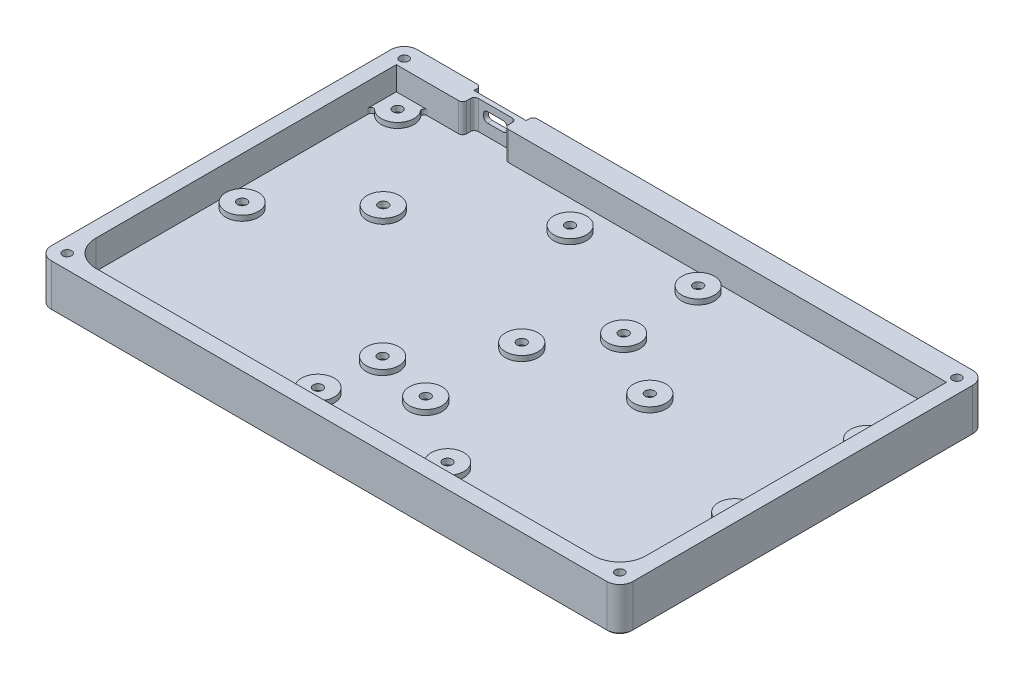
SolidWorks part; units mm, degrees
ref_plane "Front Plane" through (0, 0, 0) normal (0, 0, 1) x (1, 0, 0)
ref_plane "Top Plane" through (0, 0, 0) normal (0, 1, 0) x (1, 0, 0)
ref_plane "Right Plane" through (0, 0, 0) normal (1, 0, 0) x (0, 0, -1)
sketch "Sketch1" plane through (0, 0, 0) normal (0, 1, 0) x (1, 0, 0)
  line L1 (0, 0) -> (222.53, 0)
  line L2 (0, 0) -> (0, 140)
  line L3 (0, 140) -> (222.53, 140)
  line L4 (222.53, 0) -> (222.53, 140)
  dimension "D1" = 140
  dimension "D2" = 222.53
extrude "Baseplate" add sketch "Sketch1" along normal blind 5.6
sketch "Sketch2" plane through (0, 5.6, 0) normal (0, 1, 0) x (1, 0, 0)
  line L1 (0, 140) -> (222.53, 140)
  line L2 (0, 140) -> (0, 0)
  line L3 (0, 0) -> (222.53, 0)
  line L4 (222.53, 140) -> (222.53, 0)
  line L5 (206.53, 6) -> (16, 6)
  line L6 (216.53, 16) -> (216.53, 131)
  line L7 (216.53, 131) -> (6, 131)
  line L8 (6, 16) -> (6, 131)
  arc A0 (206.53, 6) -> (216.53, 16) centre (206.53, 16) ccw
  arc A1 (16, 6) -> (6, 16) centre (16, 16) cw
  dimension "D5" = 10
  dimension "D1" = 6
  dimension "D2" = 6
  dimension "D3" = 6
  dimension "D4" = 9
extrude "Sidewalls" add sketch "Sketch2" along normal blind 11
sketch "Sketch3" plane through (0, 16.6, 0) normal (0, 1, 0) x (1, 0, 0)
  line L0 (216.53, 131) -> (6, 131) construction
  line L1 (31.38, 131) -> (47.38, 131)
  line L2 (31.38, 131) -> (31.38, 135.5)
  line L3 (31.38, 135.5) -> (47.38, 135.5)
  line L4 (47.38, 131) -> (47.38, 135.5)
  line L5 (0, 140) -> (0, 0) construction
  line L7 (39.38, 135.5) -> (39.38, 131) construction
  dimension "D1" = 16
  dimension "D2" = 4.5
  dimension "D3" = 39.38
extrude "USB Relief" cut sketch "Sketch3" against normal up to surface (11 mm away) up to face at (111.265, 5.6, -50.3096)
sketch "Sketch6" plane through (0, 5.6, 0) normal (0, 1, 0) x (1, 0, 0)
  circle A0 centre (12, 125.5) radius 6.25
  circle A1 centre (83.5, 120) radius 6.25
  circle A2 centre (41, 91) radius 6.25
  circle A3 centre (13, 65) radius 6.25
  circle A4 centre (91, 40.75) radius 6.25
  circle A5 centre (138.5, 18.125) radius 6.25
  circle A6 centre (89, 18) radius 6.25
  circle A7 centre (112.5, 35.75) radius 6.25
  circle A8 centre (113, 72) radius 6.25
  circle A9 centre (210, 56.5) radius 6.25
  circle A10 centre (154.5, 79.5) radius 6.25
  circle A11 centre (211, 106) radius 6.25
  circle A12 centre (128, 124.5) radius 6.25
  circle A13 centre (129.5, 94.5) radius 6.25
  dimension "D1" = 12.5
extrude "PCB Support" add sketch "Sketch6" along normal blind 2
sketch "Sketch15" plane through (0, 5.6, 0) normal (0, 1, 0) x (1, 0, 0)
  line L1 (6, 131) -> (12, 131)
  line L2 (6, 131) -> (6, 125.5)
  line L3 (6, 125.5) -> (12, 125.5)
  line L4 (12, 131) -> (12, 125.5)
  arc A0 (6, 123.75) -> (14.9686, 131) centre (12, 125.5) ccw construction
extrude "Corner Fill" add sketch "Sketch15" along normal up to vertex
fillet "Fillet3" radius 1 2 edges at (6, 6.6, -123.75) (14.9686, 6.6, -131)
sketch "Sketch4" plane through (0, 5.6, 0) normal (0, 1, 0) x (1, 0, 0)
  line L1 (9.1, 128.4) -> (14.9, 128.4)
  line L2 (9.1, 128.4) -> (9.1, 122.6)
  line L3 (9.1, 122.6) -> (14.9, 122.6)
  line L4 (14.9, 128.4) -> (14.9, 122.6)
  line L5 (9.1, 128.4) -> (14.9, 122.6) construction
  line L6 (9.1, 122.6) -> (14.9, 128.4) construction
  line L7 (80.6, 122.9) -> (86.4, 122.9)
  line L8 (80.6, 122.9) -> (80.6, 117.1)
  line L9 (80.6, 117.1) -> (86.4, 117.1)
  line L10 (86.4, 122.9) -> (86.4, 117.1)
  line L11 (80.6, 122.9) -> (86.4, 117.1) construction
  line L12 (80.6, 117.1) -> (86.4, 122.9) construction
  line L13 (10.1, 62.1) -> (15.9, 62.1)
  line L14 (10.1, 62.1) -> (10.1, 67.9)
  line L15 (10.1, 67.9) -> (15.9, 67.9)
  line L16 (15.9, 62.1) -> (15.9, 67.9)
  line L17 (10.1, 62.1) -> (15.9, 67.9) construction
  line L18 (10.1, 67.9) -> (15.9, 62.1) construction
  line L19 (88.1, 37.85) -> (93.9, 37.85)
  line L20 (88.1, 37.85) -> (88.1, 43.65)
  line L21 (88.1, 43.65) -> (93.9, 43.65)
  line L22 (93.9, 37.85) -> (93.9, 43.65)
  line L23 (88.1, 37.85) -> (93.9, 43.65) construction
  line L24 (88.1, 43.65) -> (93.9, 37.85) construction
  line L25 (110.1, 69.1) -> (115.9, 69.1)
  line L26 (110.1, 69.1) -> (110.1, 74.9)
  line L27 (110.1, 74.9) -> (115.9, 74.9)
  line L28 (115.9, 69.1) -> (115.9, 74.9)
  line L29 (110.1, 69.1) -> (115.9, 74.9) construction
  line L30 (110.1, 74.9) -> (115.9, 69.1) construction
  line L31 (135.6, 15.225) -> (141.4, 15.225)
  line L32 (135.6, 15.225) -> (135.6, 21.025)
  line L33 (135.6, 21.025) -> (141.4, 21.025)
  line L34 (141.4, 15.225) -> (141.4, 21.025)
  line L35 (135.6, 15.225) -> (141.4, 21.025) construction
  line L36 (135.6, 21.025) -> (141.4, 15.225) construction
  line L37 (91.9, 15.1) -> (86.1, 15.1)
  line L38 (91.9, 15.1) -> (91.9, 20.9)
  line L39 (91.9, 20.9) -> (86.1, 20.9)
  line L40 (86.1, 15.1) -> (86.1, 20.9)
  line L41 (91.9, 15.1) -> (86.1, 20.9) construction
  line L42 (91.9, 20.9) -> (86.1, 15.1) construction
  line L43 (212.9, 59.4) -> (207.1, 59.4)
  line L44 (212.9, 59.4) -> (212.9, 53.6)
  line L45 (212.9, 53.6) -> (207.1, 53.6)
  line L46 (207.1, 59.4) -> (207.1, 53.6)
  line L47 (212.9, 59.4) -> (207.1, 53.6) construction
  line L48 (212.9, 53.6) -> (207.1, 59.4) construction
  line L49 (126.6, 91.6) -> (132.4, 91.6)
  line L50 (126.6, 91.6) -> (126.6, 97.4)
  line L51 (126.6, 97.4) -> (132.4, 97.4)
  line L52 (132.4, 91.6) -> (132.4, 97.4)
  line L53 (126.6, 91.6) -> (132.4, 97.4) construction
  line L54 (126.6, 97.4) -> (132.4, 91.6) construction
  line L55 (125.1, 127.4) -> (130.9, 127.4)
  line L56 (125.1, 127.4) -> (125.1, 121.6)
  line L57 (125.1, 121.6) -> (130.9, 121.6)
  line L58 (130.9, 127.4) -> (130.9, 121.6)
  line L59 (125.1, 127.4) -> (130.9, 121.6) construction
  line L60 (125.1, 121.6) -> (130.9, 127.4) construction
  line L61 (213.9, 103.1) -> (208.1, 103.1)
  line L62 (213.9, 103.1) -> (213.9, 108.9)
  line L63 (213.9, 108.9) -> (208.1, 108.9)
  line L64 (208.1, 103.1) -> (208.1, 108.9)
  line L65 (213.9, 103.1) -> (208.1, 108.9) construction
  line L66 (213.9, 108.9) -> (208.1, 103.1) construction
  line L67 (38.1, 88.1) -> (43.9, 88.1)
  line L68 (38.1, 88.1) -> (38.1, 93.9)
  line L69 (38.1, 93.9) -> (43.9, 93.9)
  line L70 (43.9, 88.1) -> (43.9, 93.9)
  line L71 (38.1, 88.1) -> (43.9, 93.9) construction
  line L72 (38.1, 93.9) -> (43.9, 88.1) construction
  line L73 (109.6, 32.85) -> (115.4, 32.85)
  line L74 (109.6, 32.85) -> (109.6, 38.65)
  line L75 (109.6, 38.65) -> (115.4, 38.65)
  line L76 (115.4, 32.85) -> (115.4, 38.65)
  line L77 (109.6, 32.85) -> (115.4, 38.65) construction
  line L78 (109.6, 38.65) -> (115.4, 32.85) construction
  line L79 (151.6, 76.6) -> (157.4, 76.6)
  line L80 (151.6, 76.6) -> (151.6, 82.4)
  line L81 (151.6, 82.4) -> (157.4, 82.4)
  line L82 (157.4, 76.6) -> (157.4, 82.4)
  line L83 (151.6, 76.6) -> (157.4, 82.4) construction
  line L84 (151.6, 82.4) -> (157.4, 76.6) construction
  point P0 (12, 125.5)
  point P5 (41, 91)
  point P6 (83.5, 120)
  point P12 (13, 65)
  point P18 (91, 40.75)
  point P24 (113, 72)
  point P30 (138.5, 18.125)
  point P35 (112.5, 35.75)
  point P36 (89, 18)
  point P42 (210, 56.5)
  point P48 (129.5, 94.5)
  point P54 (128, 124.5)
  point P60 (211, 106)
  point P65 (154.5, 79.5)
  dimension "D1" = 5.8
extrude "Nut Cutout" cut sketch "Sketch4" against normal blind 1.8 from offset 0.2 offset against normal yes
sketch "Sketch7" plane through (0, 7.6, 0) normal (0, 1, 0) x (1, 0, 0)
  circle A0 centre (41, 91) radius 1.4
  circle A1 centre (154.5, 79.5) radius 1.4
  circle A2 centre (112.5, 35.75) radius 1.4
  dimension "D1" = 2.8
extrude "Alignment Pins" [suppressed] add sketch "Sketch7" along normal blind 2
sketch "Sketch8" plane through (0, 0, -135.5) normal (0, 0, 1) x (1, 0, 0)
  line L1 (31.38, 5.6) -> (47.38, 5.6)
  line L2 (31.38, 5.6) -> (31.38, 16.6) construction
  line L3 (31.38, 16.6) -> (47.38, 16.6)
  line L4 (47.38, 5.6) -> (47.38, 16.6) construction
  line L5 (47.38, 16.6) -> (49.38, 16.6)
  line L6 (47.38, 16.6) -> (47.38, 5.6) construction
  line L7 (47.38, 5.6) -> (49.38, 5.6)
  line L8 (49.38, 16.6) -> (49.38, 5.6)
  line L9 (31.38, 16.6) -> (29.38, 16.6)
  line L10 (31.38, 16.6) -> (31.38, 5.6) construction
  line L11 (31.38, 5.6) -> (29.38, 5.6)
  line L12 (29.38, 16.6) -> (29.38, 5.6)
  dimension "D1" = 2
extrude "Thin USB Wall" cut sketch "Sketch8" against normal up to next from offset 1.8 offset against normal yes
hole_wizard "M3 Clearance Hole1" positions "3DSketch1" profile "Sketch9" hole size "M3" standard "ANSI Metric"
sketch3d "3DSketch1"
  line L0 (12, 7.6, -125.5) -> (12, 5.6, -125.5) construction
  line L5 (113, 7.6, -72) -> (113, 5.6, -72) construction
  line L7 (91, 7.6, -40.75) -> (91, 5.6, -40.75) construction
  line L8 (89, 7.6, -18) -> (89, 5.6, -18) construction
  line L9 (138.5, 7.6, -18.125) -> (138.5, 5.6, -18.125) construction
  line L10 (210, 7.6, -56.5) -> (210, 5.6, -56.5) construction
  line L11 (83.5, 7.6, -120) -> (83.5, 5.6, -120) construction
  line L12 (128, 7.6, -124.5) -> (128, 5.6, -124.5) construction
  line L13 (211, 7.6, -106) -> (211, 5.6, -106) construction
  line L14 (129.5, 7.6, -94.5) -> (129.5, 5.6, -94.5) construction
  line L15 (13, 7.6, -65) -> (13, 5.6, -65) construction
  line L16 (41, 7.6, -91) -> (41, 5.6, -91) construction
  line L17 (112.5, 7.6, -35.75) -> (112.5, 5.6, -35.75) construction
  line L18 (154.5, 7.6, -79.5) -> (154.5, 5.6, -79.5) construction
  point P44 (12, 7.6, -125.5)
  point P64 (113, 7.6, -72)
  point P72 (91, 7.6, -40.75)
  point P76 (89, 7.6, -18)
  point P80 (138.5, 7.6, -18.125)
  point P84 (210, 7.6, -56.5)
  point P92 (83.5, 7.6, -120)
  point P96 (128, 7.6, -124.5)
  point P100 (211, 7.6, -106)
  point P104 (129.5, 7.6, -94.5)
  point P108 (13, 7.6, -65)
  point P129 (41, 7.6, -91)
  point P133 (112.5, 7.6, -35.75)
  point P137 (154.5, 7.6, -79.5)
sketch "Sketch9" plane through (12, 7.6, -125.5) normal (1, 0, 0) x (0, 0, 1)
  line L0 (0, 0) -> (0, 3.5)
  line L1 (0, 3.5) -> (1.8, 2.4185)
  line L2 (1.8, 2.4185) -> (1.8, 0)
  line L5 (1.8, 0) -> (0, 0)
  line L10 (0, 3.5) -> (-1.8, 2.4185) construction
  line L11 (0, -6.35) -> (0, 107.95) construction
  dimension "Hole Dia." = 3.6
  dimension "Hole Depth" = 3.5
  dimension "Drill Angle" = 118
hole_wizard "CSK for M3 Flat Head Machine Screw1" positions "3DSketch2" profile "Sketch11" countersink size "M3" standard "ANSI Metric" end condition through all
sketch3d "3DSketch2"
  line L1 (0, 0, -140) -> (0, 0, 0) construction
  line L2 (222.53, 0, -140) -> (0, 0, -140) construction
  line L3 (0, 0, 0) -> (222.53, 0, 0) construction
  line L4 (222.53, 0, 0) -> (222.53, 0, -140) construction
  point P0 (217.03, 0, -5.5)
  point P2 (5.5, 0, -5.5)
  point P4 (5.5, 0, -134.5)
  point P6 (217.03, 0, -134.5)
  dimension "D1" = 5.5
  dimension "D2" = 5.5
  dimension "D3" = 5.5
  dimension "D4" = 5.5
  dimension "D5" = 5.5
  dimension "D6" = 5.5
  dimension "D7" = 5.5
  dimension "D8" = 5.5
sketch "Sketch11" plane through (217.03, 0, -5.5) normal (1, 0, 0) x (0, 0, -1)
  line L0 (0, 0) -> (0, 16.6)
  line L1 (0, 16.6) -> (1.7, 16.6)
  line L2 (1.7, 16.6) -> (1.7, 3.45)
  line L3 (1.7, 3.45) -> (3.15, 2)
  line L4 (3.15, 2) -> (3.15, 0)
  line L6 (3.15, 0) -> (0, 0)
  line L7 (-1.7, 3.45) -> (-3.15, 2) construction
  line L11 (0, -6.35) -> (0, 107.95) construction
  dimension "Thru Hole Dia." = 3.4
  dimension "Thru Hole Depth" = 16.6
  dimension "C'Sink Dia." = 6.3
  dimension "C'Sink Angle" = 90
  dimension "Head Clearance" = 2
sketch "Sketch12" plane through (0, 0, -137.3) normal (0, 0, -1) x (-1, 0, 0)
  line L0 (-39.38, 14) -> (-39.38, 16.6) construction
  line L1 (-42.38, 14) -> (-36.38, 14)
  line L2 (-43.88, 12.5) -> (-43.88, 11.7)
  line L3 (-42.38, 10.2) -> (-36.38, 10.2)
  line L4 (-34.88, 12.5) -> (-34.88, 11.7)
  line L5 (-49.38, 16.6) -> (-29.38, 16.6) construction
  arc A0 (-36.38, 10.2) -> (-34.88, 11.7) centre (-36.38, 11.7) ccw
  arc A1 (-43.88, 11.7) -> (-42.38, 10.2) centre (-42.38, 11.7) ccw
  arc A2 (-42.38, 14) -> (-43.88, 12.5) centre (-42.38, 12.5) ccw
  arc A3 (-36.38, 14) -> (-34.88, 12.5) centre (-36.38, 12.5) cw
  dimension "D1" = 1.5
  dimension "D2" = 9
  dimension "D3" = 3.8
  dimension "D4" = 2.6
extrude "USB Port" cut sketch "Sketch12" against normal up to next
fillet "Fillet1" radius 5 4 edges at (222.53, 8.3, -140) (222.53, 8.3, 0) (0, 8.3, 0) (0, 8.3, -140)
fillet "Fillet2" radius 1.5 6 edges at (31.38, 11.1, -135.5) (47.38, 11.1, -135.5) (31.38, 11.1, -131) (47.38, 11.1, -131) (29.38, 11.1, -140) (49.38, 11.1, -140)
sketch "Sketch13" plane through (0, 0, 0) normal (0, -1, 0) x (1, 0, 0)
  line L1 (11.265, -130) -> (211.265, -130)
  line L2 (11.265, -130) -> (11.265, -10)
  line L3 (11.265, -10) -> (211.265, -10)
  line L4 (211.265, -130) -> (211.265, -10)
  line L8 (0, 0) -> (222.53, 0) construction
  line L9 (111.265, 0) -> (111.265, -10) construction
  line L10 (11.265, -70) -> (0, -70) construction
  line L11 (0, 0) -> (0, -140) construction
  dimension "D1" = 120
  dimension "D2" = 200
extrude "Cut-Extrude1" cut sketch "Sketch13" against normal blind 2.6
chamfer "Chamfer1" distance 0.5 angle 45 16 edges at (0, 0, -70) (1.4645, 0, -1.4645) (1.4645, 0, -138.5355) (111.265, 0, 0) (111.265, 0, -140) (221.0655, 0, -1.4645) (221.0655, 0, -138.5355) (222.53, 0, -70) (111.265, 0, -130) (211.265, 0, -70) (111.265, 0, -10) (11.265, 0, -70) (5.5, 0, -137.65) (217.03, 0, -137.65) (217.03, 0, -8.65) (5.5, 0, -8.65)
sketch "Sketch14" [suppressed] plane through (0, 0, 0) normal (0, -1, 0) x (1, 0, 0)
  line L0 (0, -5) -> (0, 22.5054)
  line L1 (3, 11.9698) -> (3, -0.4174)
  line L2 (111.265, 0) -> (111.265, -140) construction
  line L3 (5, 0) -> (217.53, 0) construction
  line L4 (217.53, -140) -> (5, -140) construction
  line L5 (0, -70) -> (222.53, -70) construction
  line L6 (0, -135) -> (0, -5) construction
  line L7 (222.53, -5) -> (222.53, -135) construction
  line L8 (219.53, 11.9698) -> (219.53, -0.4174)
  line L9 (222.53, -5) -> (222.53, 22.5054)
  line L10 (222.53, -135) -> (222.53, -162.5054)
  line L11 (219.53, -151.9698) -> (219.53, -139.5826)
  line L12 (3, -151.9698) -> (3, -139.5826)
  line L13 (0, -135) -> (0, -162.5054)
  line L14 (3, -0.4174) -> (0, -5)
  line L15 (219.53, -0.4174) -> (222.53, -5)
  line L16 (222.53, -135) -> (219.53, -139.5826)
  line L17 (0, -135) -> (3, -139.5826)
  arc A0 (5, 0) -> (0, -5) centre (5, -5) ccw construction
  circle A1 centre (20, 22.5054) radius 20
  circle A2 centre (202.53, 22.5054) radius 20
  circle A3 centre (202.53, -162.5054) radius 20
  circle A4 centre (20, -162.5054) radius 20
  dimension "D2" = 40
  dimension "D1" = 3
extrude "Boss-Extrude1" [suppressed] add sketch "Sketch14" against normal blind 1
